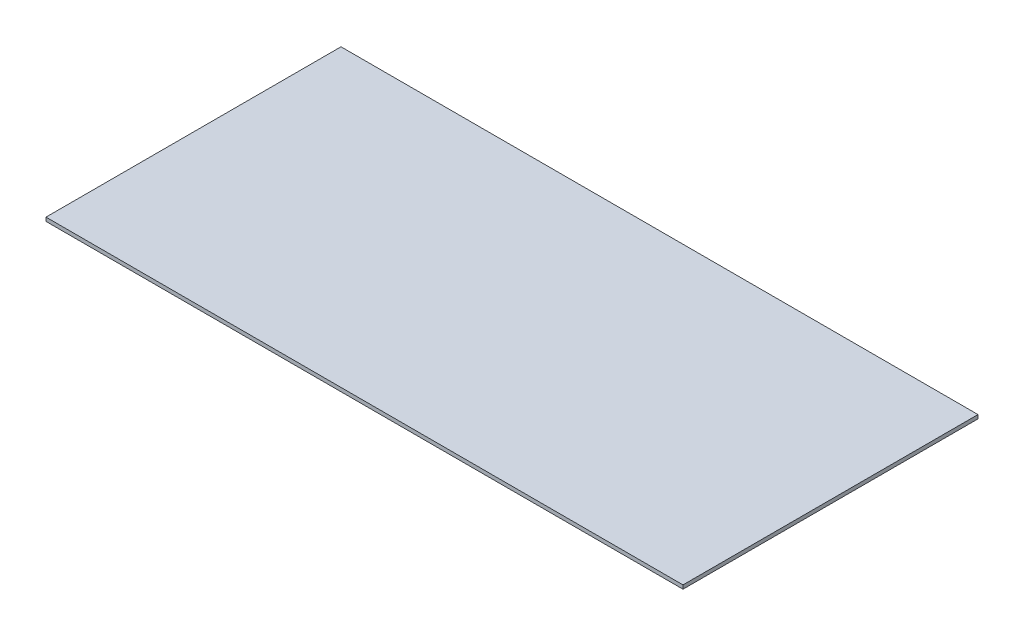
SolidWorks part; units mm, degrees
ref_plane "Front Plane" through (0, 0, 0) normal (0, 0, 1) x (1, 0, 0)
ref_plane "Top Plane" through (0, 0, 0) normal (0, 1, 0) x (1, 0, 0)
ref_plane "Right Plane" through (0, 0, 0) normal (1, 0, 0) x (0, 0, -1)
sketch "Sketch1" plane through (0, 0, 0) normal (0, 1, 0) x (1, 0, 0)
  line L1 (538.1625, -249.2375) -> (-538.1625, -249.2375)
  line L2 (538.1625, -249.2375) -> (538.1625, 249.2375)
  line L3 (538.1625, 249.2375) -> (-538.1625, 249.2375)
  line L4 (-538.1625, -249.2375) -> (-538.1625, 249.2375)
  line L5 (538.1625, -249.2375) -> (-538.1625, 249.2375) construction
  line L6 (538.1625, 249.2375) -> (-538.1625, -249.2375) construction
  point P0 (0, 0)
  dimension "D1" = 498.475
  dimension "D2" = 1076.325
extrude "Glass" add sketch "Sketch1" along normal blind 6.35
